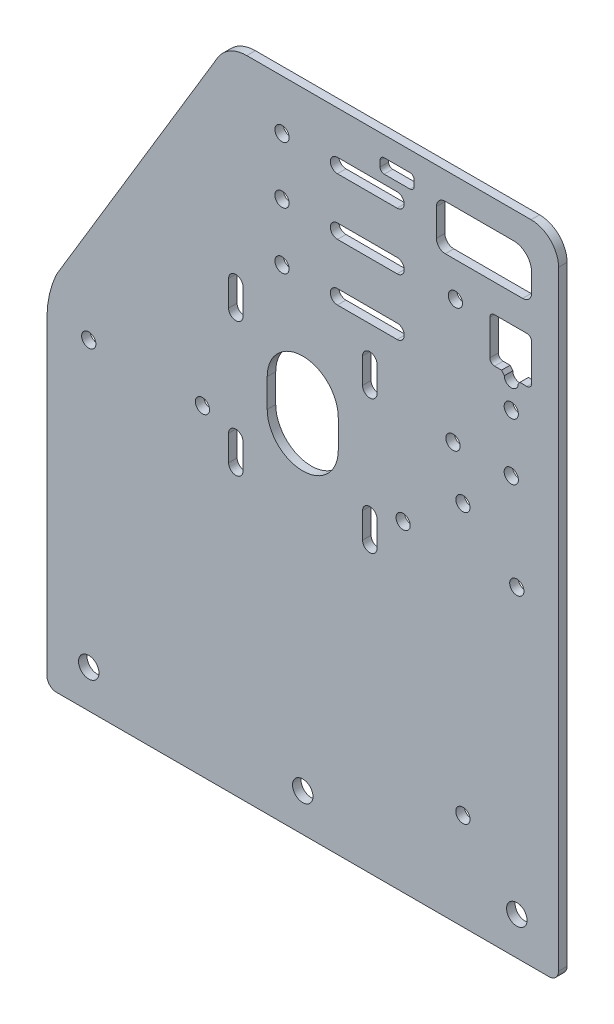
SolidWorks part; units mm, degrees
ref_plane "Front" through (0, 0, 0) normal (0, 0, 1) x (1, 0, 0)
ref_plane "Top" through (0, 0, 0) normal (0, 1, 0) x (1, 0, 0)
ref_plane "Right" through (0, 0, 0) normal (1, 0, 0) x (0, 0, -1)
sketch "Model" plane through (0, 0, 0) normal (0, 0, 1) x (1, 0, 0)
  line L0 (-86.64, 0) -> (86.64, 0)
  line L1 (-90, 112.31) -> (-90, 3.36)
  line L2 (-29.9646, 221.6756) -> (-86.6188, 127.3872)
  line L3 (-26.095, 100.21) -> (-26.095, 109.21)
  line L4 (-26.095, 147.35) -> (-26.095, 156.35)
  line L5 (-21.015, 156.35) -> (-21.015, 147.35)
  line L6 (-21.015, 109.21) -> (-21.015, 100.21)
  line L9 (21.045, 100.21) -> (21.045, 109.21)
  line L10 (21.045, 147.35) -> (21.045, 156.35)
  line L11 (26.125, 156.35) -> (26.125, 147.35)
  line L12 (26.125, 109.21) -> (26.125, 100.21)
  line L13 (27.205, 216.97) -> (27.205, 219.09)
  line L14 (76.385, 175.96) -> (75.818, 175.2497)
  line L15 (39.205, 219.09) -> (39.205, 216.97)
  line L16 (47.015, 205.17) -> (47.015, 214.86)
  line L17 (33.205, 167.44) -> (12.205, 167.44)
  line L18 (12.205, 172.44) -> (33.205, 172.44)
  line L19 (65.815, 178.1211) -> (65.815, 190.45)
  line L20 (78.855, 175.96) -> (76.385, 175.96)
  line L21 (69.945, 176.4611) -> (67.475, 176.4611)
  line L22 (33.205, 187.44) -> (12.205, 187.44)
  line L23 (67.475, 192.11) -> (78.855, 192.11)
  line L24 (80.515, 211.65) -> (80.515, 205.17)
  line L25 (80.515, 190.45) -> (80.515, 177.62)
  line L26 (12.205, 192.44) -> (33.205, 192.44)
  line L27 (77.375, 202.03) -> (50.155, 202.03)
  line L28 (90, 3.36) -> (90, 217.83)
  line L29 (33.205, 207.44) -> (12.205, 207.44)
  line L30 (70.912, 175.2497) -> (69.945, 176.4611)
  line L31 (12.205, 212.44) -> (33.205, 212.44)
  line L32 (37.765, 215.53) -> (28.645, 215.53)
  line L33 (50.155, 218) -> (74.165, 218)
  line L34 (28.645, 220.53) -> (37.765, 220.53)
  line L35 (80.33, 227.5) -> (-19.67, 227.5)
  line L36 (-90, 13.33) -> (90, 13.33) construction
  line L37 (0, 0) -> (0, 227.5) construction
  line L38 (0, 123.28) -> (0, 133.28) construction
  line L39 (-12.5, 123.28) -> (-12.5, 133.28)
  line L40 (12.5, 123.28) -> (12.5, 133.28)
  circle A0 centre (-75.285, 13.33) radius 3.6
  arc A1 (-90, 3.36) -> (-86.64, 0) centre (-86.64, 3.36) ccw
  arc A2 (-26.095, 100.21) -> (-21.015, 100.21) centre (-23.555, 100.21) ccw
  arc A3 (-21.015, 109.21) -> (-26.095, 109.21) centre (-23.555, 109.21) ccw
  arc A4 (-86.6188, 127.3872) -> (-90, 112.31) centre (-53.9604, 112.1455) ccw
  arc A5 (-19.67, 227.5) -> (-29.9646, 221.6756) centre (-19.67, 215.49) ccw
  arc A6 (-21.015, 156.35) -> (-26.095, 156.35) centre (-23.555, 156.35) ccw
  arc A7 (-26.095, 147.35) -> (-21.015, 147.35) centre (-23.555, 147.35) ccw
  circle A8 centre (-7.295, 209.94) radius 2.5
  circle A9 centre (-7.295, 189.94) radius 2.5
  circle A10 centre (-7.295, 169.94) radius 2.5
  circle A11 centre (-35.285, 113.03) radius 2.5
  circle A12 centre (-75.285, 113.03) radius 2.5
  circle A13 centre (75.315, 13.33) radius 3.6
  circle A14 centre (0, 13.33) radius 3.6
  arc A15 (86.64, 0) -> (90, 3.36) centre (86.64, 3.36) ccw
  arc A16 (21.045, 100.21) -> (26.125, 100.21) centre (23.585, 100.21) ccw
  arc A17 (26.125, 109.21) -> (21.045, 109.21) centre (23.585, 109.21) ccw
  circle A18 centre (56.355, 34.03) radius 2.5
  arc A21 (90, 217.83) -> (80.33, 227.5) centre (80.33, 217.83) ccw
  arc A22 (80.515, 211.65) -> (74.165, 218) centre (74.165, 211.65) ccw
  arc A23 (77.375, 202.03) -> (80.515, 205.17) centre (77.375, 205.17) ccw
  arc A24 (47.015, 205.17) -> (50.155, 202.03) centre (50.155, 205.17) ccw
  arc A25 (50.155, 218) -> (47.015, 214.86) centre (50.155, 214.86) ccw
  arc A26 (21.045, 147.35) -> (26.125, 147.35) centre (23.585, 147.35) ccw
  arc A27 (26.125, 156.35) -> (21.045, 156.35) centre (23.585, 156.35) ccw
  arc A28 (33.205, 207.44) -> (33.205, 212.44) centre (33.205, 209.94) ccw
  arc A29 (12.205, 212.44) -> (12.205, 207.44) centre (12.205, 209.94) ccw
  arc A30 (33.205, 187.44) -> (33.205, 192.44) centre (33.205, 189.94) ccw
  arc A31 (12.205, 192.44) -> (12.205, 187.44) centre (12.205, 189.94) ccw
  arc A32 (33.205, 167.44) -> (33.205, 172.44) centre (33.205, 169.94) ccw
  arc A33 (12.205, 172.44) -> (12.205, 167.44) centre (12.205, 169.94) ccw
  circle A34 centre (53.705, 189.94) radius 2.5
  circle A35 centre (73.365, 165.98) radius 2.5
  circle A36 centre (73.365, 145.98) radius 2.5
  circle A37 centre (52.865, 145.98) radius 2.5
  circle A38 centre (56.355, 129.03) radius 2.5
  circle A39 centre (75.315, 113.03) radius 2.5
  circle A40 centre (35.315, 113.03) radius 2.5
  arc A41 (80.515, 190.45) -> (78.855, 192.11) centre (78.855, 190.45) ccw
  arc A42 (78.855, 175.96) -> (80.515, 177.62) centre (78.855, 177.62) ccw
  arc A43 (65.815, 178.1211) -> (67.475, 176.4611) centre (67.475, 178.1211) ccw
  arc A44 (67.475, 192.11) -> (65.815, 190.45) centre (67.475, 190.45) ccw
  arc A45 (39.205, 219.09) -> (37.765, 220.53) centre (37.765, 219.09) ccw
  arc A46 (37.765, 215.53) -> (39.205, 216.97) centre (37.765, 216.97) ccw
  arc A47 (27.205, 216.97) -> (28.645, 215.53) centre (28.645, 216.97) ccw
  arc A48 (28.645, 220.53) -> (27.205, 219.09) centre (28.645, 219.09) ccw
  arc A49 (-12.5, 123.28) -> (12.5, 123.28) centre (0, 123.28) ccw
  arc A50 (12.5, 133.28) -> (-12.5, 133.28) centre (0, 133.28) ccw
  ellipse E0 centre (73.365, 175.2497) end of major axis (75.818, 175.2497) minor radius 2.453 (70.912, 175.2497) -> (75.818, 175.2497) ccw
  point P147 (0, 128.28)
  dimension "D6" = 3.36
  dimension "D7" = 12.01
  dimension "D8" = 9.67
  dimension "D9" = 36.04
  dimension "D11" = 7.2
  dimension "D12" = 13.33
  dimension "D15" = 5
  dimension "D16" = 12.5
  dimension "D1" = 180
  dimension "D2" = 227.5
  dimension "D3" = 149
  dimension "D4" = 110
  dimension "D5" = 108.95
  dimension "D10" = 100
  dimension "D13" = 14.715
  dimension "D14" = 14.685
  dimension "D17" = 10
  dimension "D18" = 123.28
  dimension "D19" = 17.56
  dimension "D20" = 97.295
  dimension "D21" = 20
  dimension "D22" = 20
  dimension "D23" = 36.295
extrude "Boss-Extrude1" add sketch "Model" along normal blind 3
